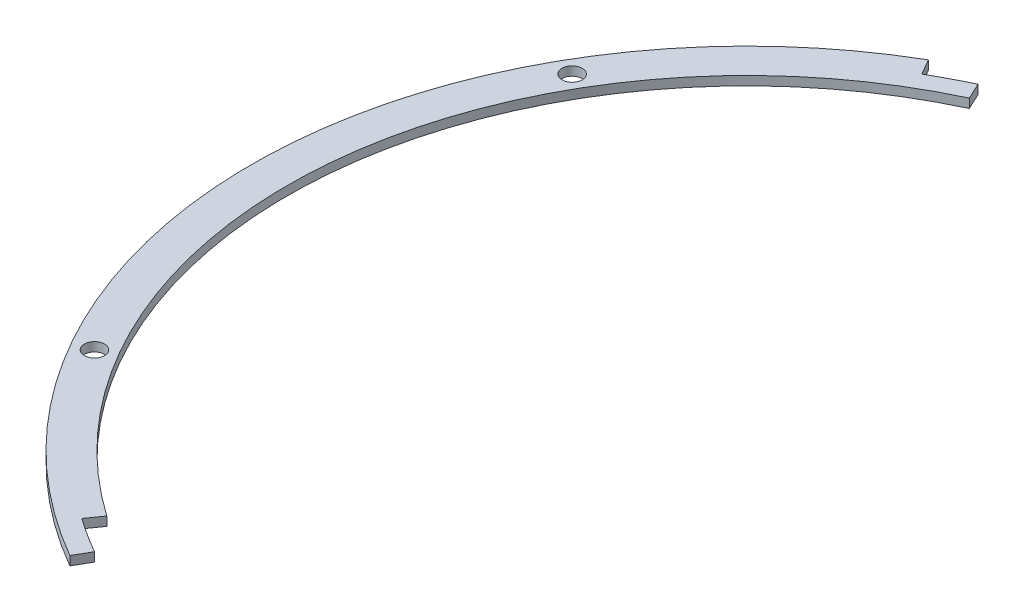
SolidWorks part; units mm, degrees
material "ABS"
ref_plane "Front Plane" through (0, 0, 0) normal (0, 0, 1) x (1, 0, 0)
ref_plane "Top Plane" through (0, 0, 0) normal (0, 1, 0) x (1, 0, 0)
ref_plane "Right Plane" through (0, 0, 0) normal (1, 0, 0) x (0, 0, -1)
sketch "Sketch1" plane through (0, 0, 0) normal (0, 1, 0) x (1, 0, 0)
  line L0 (0, 168.5) -> (0, 0) construction
  line L1 (0, 174.85) -> (0, 162.15) construction
  line L2 (0, -55) -> (0, 55) construction
  circle A0 centre (0, 0) radius 168.5 construction
  circle A1 centre (0, 168.5) radius 3.556
  circle A2 centre (145.9253, 84.25) radius 3.556
  circle A3 centre (145.9253, -84.25) radius 3.556
  circle A4 centre (0, -168.5) radius 3.556
  circle A5 centre (-145.9253, -84.25) radius 3.556
  circle A6 centre (-145.9253, 84.25) radius 3.556
  circle A7 centre (0, 0) radius 174.85
  circle A8 centre (0, 0) radius 162.15
  point P17 (0, 0)
  point P20 (0, 168.5)
  dimension "D1" = 7.112
  dimension "D2" = 337
  dimension "D6" = 12.7
  dimension "D4" = 60
  dimension "D5" = 60
  dimension "D3" = 6
extrude "Boss-Extrude1" add sketch "Sketch1" along normal blind 3.175
sketch "Sketch2" plane through (0, 0, 0) normal (0, 1, 0) x (1, 0, 0)
  line L0 (-88.9, 153.9793) -> (-84.25, 145.9253)
  line L1 (0, 0) -> (-84.25, -145.9253) construction
  line L2 (-71.2112, 152.7129) -> (-68.5276, 146.9578)
  line L3 (0, 0) -> (-75.1415, 161.1415) construction
  line L4 (0, 0) -> (-100.2898, -143.2287) construction
  line L5 (-93.0054, -132.8255) -> (-100.2898, -143.2287) construction
  line L7 (-81.075, 140.426) -> (0, 0)
  line L8 (-87.425, -151.4245) -> (-88.9, -153.9793)
  line L11 (-1.7463, 0) -> (1.7463, 0) construction
  line L12 (-73.8948, 158.4679) -> (-68.5276, 146.9578) construction
  line L13 (-96.6476, -138.0271) -> (-93.0054, -132.8255)
  line L14 (-84.25, -145.9253) -> (-87.425, -151.4245)
  line L15 (-81.075, -140.426) -> (0, 0)
  arc A0 (-81.075, -140.426) -> (-93.0054, -132.8255) centre (0, 0) cw
  circle A1 centre (0, 0) radius 174.85 construction
  arc A2 (-68.5276, 146.9578) -> (-81.075, 140.426) centre (0, 0) ccw
  arc A3 (-71.2112, 152.7129) -> (-84.25, 145.9253) centre (0, 0) ccw
  arc A4 (-88.9, 153.9793) -> (-88.9, -153.9793) centre (0, 0) cw
  arc A5 (-87.425, -151.4245) -> (-100.2898, -143.2287) centre (0, 0) cw construction
  arc A6 (-96.6476, -138.0271) -> (-84.25, -145.9253) centre (0, 0) ccw
  circle A7 centre (0, 0) radius 162.15 construction
  point P11 (-96.6476, -138.0271)
  point P24 (-71.2112, 152.7129)
  dimension "D2" = 60
  dimension "D3" = 177.8
  dimension "D1" = 120
  dimension "D4" = 5
  dimension "D5" = 5
extrude "Cut-Extrude1" cut sketch "Sketch2" along normal through all
